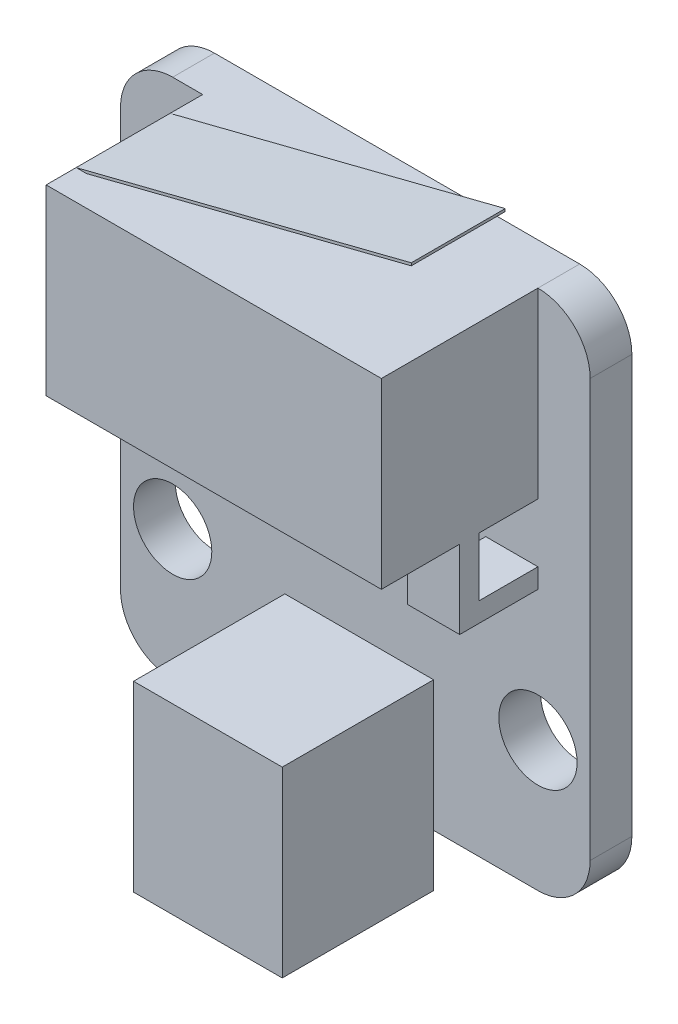
SolidWorks part; units mm, degrees
ref_plane "Front Plane" through (0, 0, 0) normal (0, 0, 1) x (1, 0, 0)
ref_plane "Top Plane" through (0, 0, 0) normal (0, 1, 0) x (1, 0, 0)
ref_plane "Right Plane" through (0, 0, 0) normal (1, 0, 0) x (0, 0, -1)
sketch "Sketch1" plane through (0, 0, 0) normal (0, 0, 1) x (1, 0, 0)
  line L0 (0, 0) -> (50000, 0) construction
  line L1 (-7, 20) -> (7, 20)
  line L2 (-9, 18) -> (-9, 2)
  line L3 (-7, 0) -> (7, 0)
  line L4 (9, 18) -> (9, 2)
  line L5 (0, 0) -> (0, 50000) construction
  circle A0 centre (7, 5) radius 1.5
  circle A1 centre (-7, 5) radius 1.5
  arc A2 (-7, 20) -> (-9, 18) centre (-7, 18) ccw
  arc A3 (7, 20) -> (9, 18) centre (7, 18) cw
  arc A4 (7, 0) -> (9, 2) centre (7, 2) ccw
  arc A5 (-9, 2) -> (-7, 0) centre (-7, 2) ccw
  point P15 (-9, 20)
  point P18 (9, 20)
  point P21 (9, 0)
  dimension "D5" = 3
  dimension "D3" = 14
  dimension "D4" = 5
  dimension "D6" = 2
  dimension "D1" = 18
  dimension "D2" = 20
extrude "Boss-Extrude1" add sketch "Sketch1" along normal blind 1.6
sketch "Sketch2" plane through (0, 0, 1.6) normal (0, 0, 1) x (1, 0, 0)
  line L2 (7, 20) -> (-7, 20) construction
  line L3 (7, 20) -> (-5.85, 20)
  line L4 (7, 20) -> (7, 10)
  line L5 (7, 10) -> (-5.85, 10)
  line L6 (-5.85, 20) -> (-5.85, 10)
  line L7 (9, 2) -> (9, 18) construction
  line M5 (7, 20) -> (-7, 20)
  dimension "D2" = 12.85
  dimension "D3" = 10
  dimension "D4" = 2
extrude "Boss-Extrude2" add sketch "Sketch2" along normal blind 6 contours L6 L5 L4 M5
sketch "Sketch3" plane through (0, 0, 7.6) normal (0, 0, 1) x (1, 0, 0)
  line L0 (7, 10) -> (-5.85, 10) construction
  line L1 (-5.85, 10) -> (7, 10)
  line L2 (-5.85, 10) -> (-5.85, 13)
  line L3 (-5.85, 13) -> (7, 13)
  line L4 (7, 10) -> (7, 13)
  line L5 (-5.85, 20) -> (-5.85, 10) construction
  line L6 (7, 20) -> (7, 10) construction
  dimension "D1" = 3
extrude "Cut-Extrude1" cut sketch "Sketch3" against normal blind 3
sketch "Sketch4" plane through (0, 0, 4.6) normal (0, 0, 1) x (1, 0, 0)
  line L0 (7, 11.5) -> (5, 11.5)
  line L1 (7, 10) -> (7, 13) construction
  line L2 (-5.85, 11.5) -> (-3.85, 11.5)
  line L3 (-5.85, 13) -> (-5.85, 10) construction
  line L4 (7, 13) -> (-5.85, 13) construction
  line L5 (-3.85, 13) -> (-0.425, 13)
  line L6 (-3.85, 13) -> (-3.85, 10)
  line L7 (-3.85, 10) -> (-0.425, 10)
  line L8 (-0.425, 13) -> (-0.425, 10)
  line L9 (-5.85, 10) -> (7, 10) construction
  line L11 (5, 13) -> (1.575, 13)
  line L12 (5, 13) -> (5, 10)
  line L13 (5, 10) -> (1.575, 10)
  line L14 (1.575, 13) -> (1.575, 10)
  line M2 (-5.85, 10) -> (7, 10)
  line M4 (7, 13) -> (-5.85, 13)
  dimension "D1" = 2
  dimension "D2" = 2
  dimension "D3" = 3.425
  dimension "D4" = 3.425
extrude "Cut-Extrude3" cut sketch "Sketch4" against normal blind 3 contours L14 L12 M4 M2 | L8 L6 M4 M2
sketch "Sketch5" plane through (7, 0, 0) normal (1, 0, 0) x (0, 0, -1)
  line L0 (-4.2467, 10.75) -> (-1.6, 10.75)
  line L1 (-4.6, 13) -> (-7.6, 13) construction
  line L5 (-1.6, 20) -> (-1.6, 10) construction
  line L7 (-3.85, 13) -> (-1.6, 13)
  line L8 (-3.85, 13) -> (-3.85, 10.75)
  line L9 (-3.85, 10.75) -> (-1.6, 10.75)
  line L10 (-1.6, 13) -> (-1.6, 10.75)
  line M4 (-1.6, 10) -> (-1.6, 20)
  dimension "D1" = 2.25
extrude "Cut-Extrude4" cut sketch "Sketch5" against normal through all contours L7 L8 L0 M4
sketch "Sketch10" plane through (0, 0, 7.6) normal (0, 0, 1) x (1, 0, 0)
  line L0 (-5.85, 20) -> (6.995, 23.2622)
  line L2 (-5.45, 20) -> (6.995, 23.1606)
  line L3 (7, 20) -> (-5.85, 20) construction
  line L4 (-5.85, 20) -> (-5.45, 20)
  line L5 (6.995, 23.2622) -> (6.995, 23.1606)
  line L6 (-5.85, 20) -> (-5.45, 20)
  dimension "D1" = 0.4
  dimension "D2" = 14.25
  dimension "D3" = 12.445
extrude "Boss-Extrude4" add sketch "Sketch10" against normal blind 4.75
sketch "Sketch11" plane through (0, 20, 0) normal (0, 1, 0) x (1, 0, 0)
  line L0 (-5.85, -7.6) -> (-5.85, -2.85) construction
  line L1 (7, -7.6) -> (-5.85, -7.6)
  line L2 (7, -7.6) -> (7, -6.45)
  line L3 (7, -6.45) -> (-5.85, -6.45)
  line L4 (-5.85, -7.6) -> (-5.85, -6.45)
  dimension "D1" = 1.15
extrude "Cut-Extrude8" cut sketch "Sketch11" along normal blind 4.75
sketch "草图1" plane through (0, 0, 1.6) normal (0, 0, 1) x (1, 0, 0)
  line L0 (-7, 0) -> (7, 0) construction
  line L1 (-2.7, 5) -> (3, 5)
  line L2 (-2.7, 5) -> (-2.7, -2)
  line L3 (-2.7, -2) -> (3, -2)
  line L4 (3, 5) -> (3, -2)
  line L5 (9, 2) -> (9, 18) construction
  dimension "D1" = 5.7
  dimension "D2" = 7
  dimension "D3" = 2
  dimension "D4" = 6
extrude "凸台-拉伸1" add sketch "草图1" along normal blind 5.8
